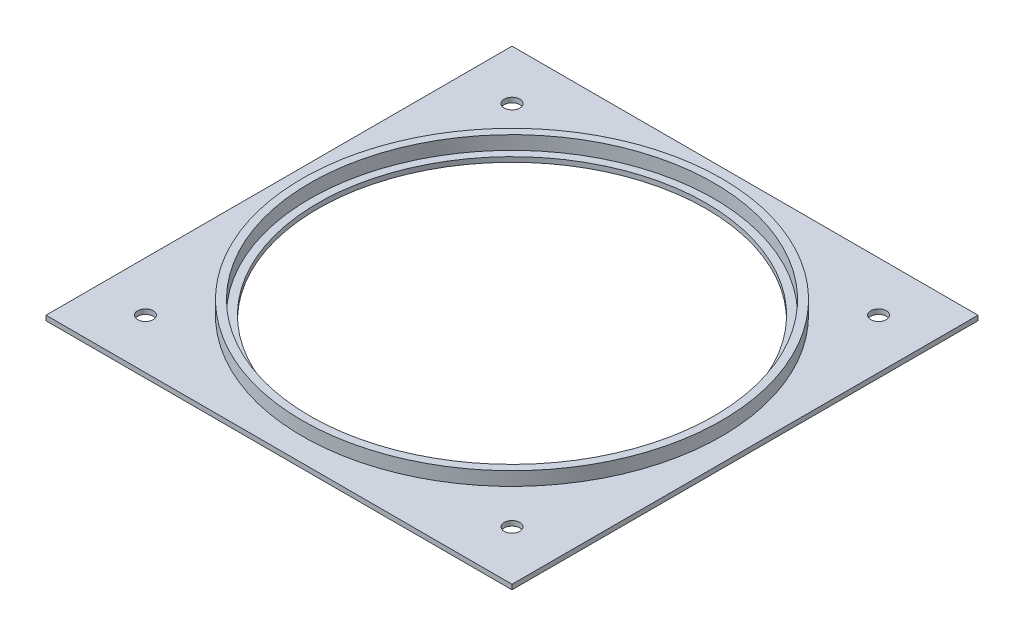
SolidWorks part; units mm, degrees
material "Alloy Steel"
ref_plane "Front Plane" through (0, 0, 0) normal (0, 0, 1) x (1, 0, 0)
ref_plane "Top Plane" through (0, 0, 0) normal (0, 1, 0) x (1, 0, 0)
ref_plane "Right Plane" through (0, 0, 0) normal (1, 0, 0) x (0, 0, -1)
sketch "Sketch1" plane through (0, 0, 0) normal (0, 1, 0) x (1, 0, 0)
  line L1 (-76.2, -76.2) -> (76.2, -76.2)
  line L2 (-76.2, -76.2) -> (-76.2, 76.2)
  line L3 (-76.2, 76.2) -> (76.2, 76.2)
  line L4 (76.2, -76.2) -> (76.2, 76.2)
  line L5 (-76.2, -76.2) -> (76.2, 76.2) construction
  line L6 (-76.2, 76.2) -> (76.2, -76.2) construction
  circle A0 centre (0, 0) radius 63.5
  circle A1 centre (-59.944, 59.944) radius 2.54
  circle A2 centre (59.944, 59.944) radius 2.54
  circle A3 centre (59.944, -59.944) radius 2.54
  circle A4 centre (-59.944, -59.944) radius 2.54
  point P18 (0, 0)
  dimension "D1" = 127
  dimension "D4" = 5.08
  dimension "D5" = 119.888
  dimension "D2" = 152.4
  dimension "D3" = 152.4
  dimension "D6" = 4
extrude "Boss-Extrude1" add sketch "Sketch1" along normal blind 1.5875
sketch "Sketch2" plane through (0, 1.5875, 0) normal (0, 1, 0) x (1, 0, 0)
  circle A0 centre (0, 0) radius 63.5 construction
  circle A1 centre (0, 0) radius 63.5
  circle A2 centre (0, 0) radius 66.04
  circle A3 centre (0, 0) radius 68.58
  dimension "D1" = 2.54
  dimension "D2" = 2.54
extrude "Boss-Extrude2" add sketch "Sketch2" along normal blind 4.445 contours A3 A2
